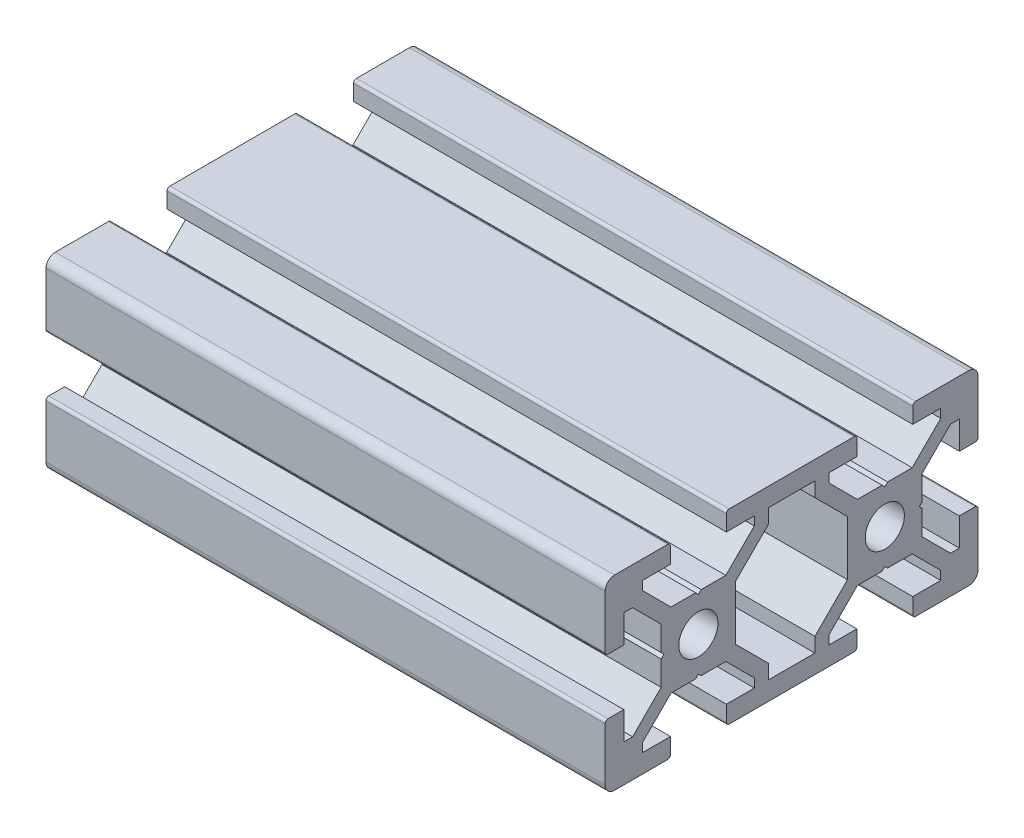
SolidWorks part; units mm, degrees
material "1060 Alloy"
ref_plane "Front Plane" through (0, 0, 0) normal (0, 0, 1) x (1, 0, 0)
ref_plane "Top Plane" through (0, 0, 0) normal (0, 1, 0) x (1, 0, 0)
ref_plane "Right Plane" through (0, 0, 0) normal (1, 0, 0) x (0, 0, -1)
sketch "Sketch1" plane through (0, 0, 0) normal (0, 0, 1) x (1, 0, 0)
  line L0 (-30, 0) -> (30, 0)
  dimension "D1" = 60
other "Structural Member1"
ref_plane "Plane1" through (-30, 0, 0) normal (1, 0, 0) x (0, 1, 0)
sketch "Sketch11" plane through (-30, 0, 0) normal (1, 0, 0) x (0, 1, 0)
  line L0 (-9, -20) -> (-3.3, -20)
  line L1 (-3, -19.7) -> (-3, -18)
  line L2 (-3, -18) -> (-6, -18)
  line L3 (-6, -18) -> (-6, -17.0607)
  line L4 (-6, -17.0607) -> (-2.9393, -14)
  line L5 (-2.9393, -14) -> (-0.3, -14)
  line L6 (-0.3, -14) -> (0, -13.7)
  line L7 (0, -13.7) -> (0.3, -14)
  line L8 (0.3, -14) -> (2.9393, -14)
  line L9 (2.9393, -14) -> (6, -17.0607)
  line L10 (6, -17.0607) -> (6, -18)
  line L11 (6, -18) -> (3, -18)
  line L12 (3, -18) -> (3, -19.7)
  line L13 (3.3, -20) -> (9, -20)
  line L14 (10, -19) -> (10, -13.3)
  line L15 (9.7, -13) -> (8, -13)
  line L16 (8, -13) -> (8, -16)
  line L17 (8, -16) -> (7.0607, -16)
  line L18 (7.0607, -16) -> (4, -12.9393)
  line L19 (4, -12.9393) -> (4, -10.3)
  line L20 (4, -10.3) -> (3.7, -10)
  line L21 (3.7, -10) -> (4, -9.7)
  line L22 (4, -9.7) -> (4, -7.0607)
  line L23 (4, -7.0607) -> (7.0607, -4)
  line L24 (7.0607, -4) -> (8, -4)
  line L25 (8, -4) -> (8, -7)
  line L26 (8, -7) -> (9.7, -7)
  line L27 (10, -6.7) -> (10, 6.7)
  line L28 (9.7, 7) -> (8, 7)
  line L29 (8, 7) -> (8, 4)
  line L30 (8, 4) -> (7.0607, 4)
  line L31 (7.0607, 4) -> (4, 7.0607)
  line L32 (4, 7.0607) -> (4, 9.7)
  line L33 (4, 9.7) -> (3.7, 10)
  line L34 (3.7, 10) -> (4, 10.3)
  line L35 (4, 10.3) -> (4, 12.9393)
  line L36 (4, 12.9393) -> (7.0607, 16)
  line L37 (7.0607, 16) -> (8, 16)
  line L38 (8, 16) -> (8, 13)
  line L39 (8, 13) -> (9.7, 13)
  line L40 (10, 13.3) -> (10, 19)
  line L41 (9, 20) -> (3.3, 20)
  line L42 (3, 19.7) -> (3, 18)
  line L43 (3, 18) -> (6, 18)
  line L44 (6, 18) -> (6, 17.0607)
  line L45 (6, 17.0607) -> (2.9393, 14)
  line L46 (2.9393, 14) -> (0.3, 14)
  line L47 (0.3, 14) -> (0, 13.7)
  line L48 (0, 13.7) -> (-0.3, 14)
  line L49 (-0.3, 14) -> (-2.9393, 14)
  line L50 (-2.9393, 14) -> (-6, 17.0607)
  line L51 (-6, 17.0607) -> (-6, 18)
  line L52 (-6, 18) -> (-3, 18)
  line L53 (-3, 18) -> (-3, 19.7)
  line L54 (-3.3, 20) -> (-9, 20)
  line L55 (-10, 19) -> (-10, 13.3)
  line L56 (-9.7, 13) -> (-8, 13)
  line L57 (-8, 13) -> (-8, 16)
  line L58 (-8, 16) -> (-7.0607, 16)
  line L59 (-7.0607, 16) -> (-4, 12.9393)
  line L60 (-4, 12.9393) -> (-4, 10.3)
  line L61 (-4, 10.3) -> (-3.7, 10)
  line L62 (-3.7, 10) -> (-4, 9.7)
  line L63 (-4, 9.7) -> (-4, 7.0607)
  line L64 (-4, 7.0607) -> (-7.0607, 4)
  line L65 (-7.0607, 4) -> (-8, 4)
  line L66 (-8, 4) -> (-8, 7)
  line L67 (-8, 7) -> (-9.7, 7)
  line L68 (-10, 6.7) -> (-10, -6.7)
  line L69 (-9.7, -7) -> (-8, -7)
  line L70 (-8, -7) -> (-8, -4)
  line L71 (-8, -4) -> (-7.0607, -4)
  line L72 (-7.0607, -4) -> (-4, -7.0607)
  line L73 (-4, -7.0607) -> (-4, -9.7)
  line L74 (-4, -9.7) -> (-3.7, -10)
  line L75 (-3.7, -10) -> (-4, -10.3)
  line L76 (-4, -10.3) -> (-4, -12.9393)
  line L77 (-4, -12.9393) -> (-7.0607, -16)
  line L78 (-7.0607, -16) -> (-8, -16)
  line L79 (-8, -16) -> (-8, -13)
  line L80 (-8, -13) -> (-9.7, -13)
  line L81 (-10, -13.3) -> (-10, -19)
  line L82 (-8, -2.5) -> (-6.4393, -2.5)
  line L83 (-6.4393, -2.5) -> (-2.9393, -6)
  line L84 (-2.9393, -6) -> (2.9393, -6)
  line L85 (2.9393, -6) -> (6.4393, -2.5)
  line L86 (6.4393, -2.5) -> (8, -2.5)
  line L87 (8, -2.5) -> (8, 2.5)
  line L88 (8, 2.5) -> (6.4393, 2.5)
  line L89 (6.4393, 2.5) -> (2.9393, 6)
  line L90 (2.9393, 6) -> (-2.9393, 6)
  line L91 (-2.9393, 6) -> (-6.4393, 2.5)
  line L92 (-6.4393, 2.5) -> (-8, 2.5)
  line L93 (-8, 2.5) -> (-8, -2.5)
  arc A0 (-10, -19) -> (-9, -20) centre (-9, -19) ccw
  arc A1 (-3.3, -20) -> (-3, -19.7) centre (-3.3, -19.7) ccw
  arc A2 (3, -19.7) -> (3.3, -20) centre (3.3, -19.7) ccw
  arc A3 (9, -20) -> (10, -19) centre (9, -19) ccw
  arc A4 (10, -13.3) -> (9.7, -13) centre (9.7, -13.3) ccw
  arc A5 (9.7, -7) -> (10, -6.7) centre (9.7, -6.7) ccw
  arc A6 (10, 6.7) -> (9.7, 7) centre (9.7, 6.7) ccw
  arc A7 (9.7, 13) -> (10, 13.3) centre (9.7, 13.3) ccw
  arc A8 (10, 19) -> (9, 20) centre (9, 19) ccw
  arc A9 (3.3, 20) -> (3, 19.7) centre (3.3, 19.7) ccw
  arc A10 (-3, 19.7) -> (-3.3, 20) centre (-3.3, 19.7) ccw
  arc A11 (-9, 20) -> (-10, 19) centre (-9, 19) ccw
  arc A12 (-10, 13.3) -> (-9.7, 13) centre (-9.7, 13.3) ccw
  arc A13 (-9.7, 7) -> (-10, 6.7) centre (-9.7, 6.7) ccw
  arc A14 (-10, -6.7) -> (-9.7, -7) centre (-9.7, -6.7) ccw
  arc A15 (-9.7, -13) -> (-10, -13.3) centre (-9.7, -13.3) ccw
  circle A16 centre (0, 10) radius 2.1
  circle A17 centre (0, -10) radius 2.1
  point P131 (0, 0)
  dimension "D1" = 8
  dimension "D2" = 8
  dimension "D3" = 10.3
  dimension "D4" = 18
  dimension "D5" = 10.3
  dimension "D6" = 18
  dimension "D7" = 4.2
  dimension "D8" = 10
  dimension "D9" = 4.2
  dimension "D10" = 10
  dimension "D11" = 40
  dimension "D12" = 20
